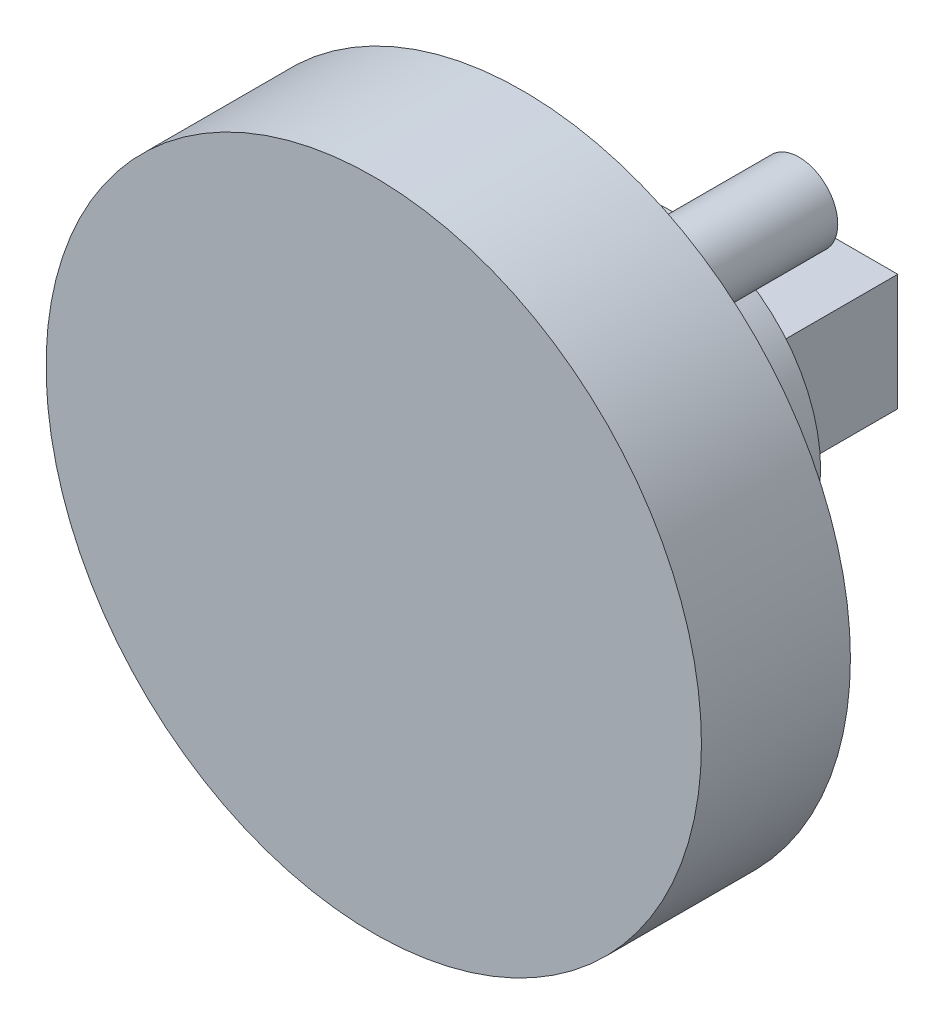
SolidWorks part; units mm, degrees
ref_plane "Front Plane" through (0, 0, 0) normal (0, 0, 1) x (1, 0, 0)
ref_plane "Top Plane" through (0, 0, 0) normal (0, 1, 0) x (1, 0, 0)
ref_plane "Right Plane" through (0, 0, 0) normal (1, 0, 0) x (0, 0, -1)
sketch "Sketch1" plane through (0, 0, 0) normal (0, 0, 1) x (1, 0, 0)
  circle A0 centre (0, 0) radius 22
  dimension "D1" = 44
extrude "Boss-Extrude1" add sketch "Sketch1" along normal blind 10
sketch "Sketch3" plane through (0, 0, 0) normal (0, 0, -1) x (-1, 0, 0)
  circle A0 centre (0, 0) radius 10
  dimension "D1" = 20
extrude "Boss-Extrude2" add sketch "Sketch3" along normal blind 10
sketch "Sketch4" plane through (0, 0, 0) normal (0, 0, -1) x (-1, 0, 0)
  line L0 (22, 0) -> (19.7, 0) construction
  line L1 (19.7, 0) -> (17.1, 0) construction
  circle A0 centre (0, 0) radius 22 construction
  circle A1 centre (17.1, 0) radius 2.6
  circle A2 centre (-8.55, -14.809) radius 2.6
  circle A3 centre (-8.55, 14.809) radius 2.6
  dimension "D1" = 2.3
  dimension "D2" = 2.6
  dimension "D3" = 3
extrude "Boss-Extrude3" add sketch "Sketch4" along normal blind 10
sketch "Sketch5" plane through (0, 0, -10) normal (0, 0, -1) x (-1, 0, 0)
  point P0 (0, 0)
sketch "Sketch7" plane through (0, 0, -10) normal (0, 0, -1) x (-1, 0, 0)
  line L1 (-5.177, -3.9115) -> (5.177, -3.9115)
  line L2 (-5.177, -3.9115) -> (-5.177, 3.9115)
  line L3 (-5.177, 3.9115) -> (5.177, 3.9115)
  line L4 (5.177, -3.9115) -> (5.177, 3.9115)
  line L5 (-5.177, -3.9115) -> (5.177, 3.9115) construction
  line L6 (-5.177, 3.9115) -> (5.177, -3.9115) construction
  point P0 (0, 0)
extrude "Boss-Extrude4" add sketch "Sketch7" along normal blind 10
